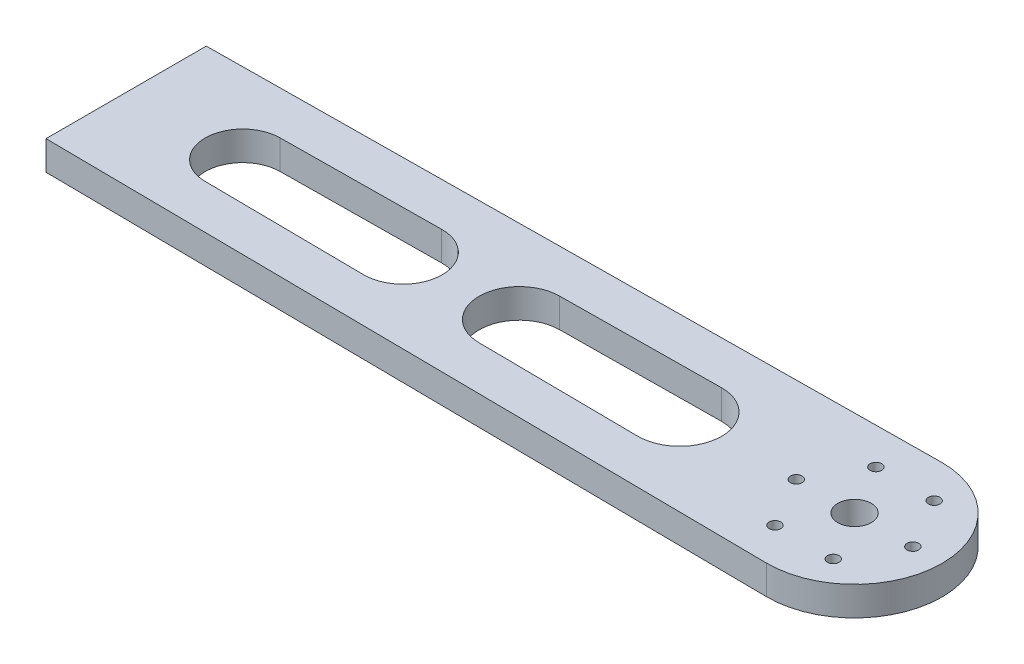
SolidWorks part; units mm, degrees
material "Acrylic (Medium-high impact)"
ref_plane "Front Plane" through (0, 0, 0) normal (0, 0, 1) x (1, 0, 0)
ref_plane "Top Plane" through (0, 0, 0) normal (0, 1, 0) x (1, 0, 0)
ref_plane "Right Plane" through (0, 0, 0) normal (1, 0, 0) x (0, 0, -1)
sketch "Sketch1" plane through (0, 0, 0) normal (0, 1, 0) x (1, 0, 0)
  line L0 (-216.3821, 37.4794) -> (33.318, 39.9538)
  line L1 (-216.3874, -17.5206) -> (33.3122, -20.0432)
  line L2 (-176.5126, 22.8737) -> (-121.518, 23.4187)
  line L3 (-216.3821, 37.4794) -> (-216.3874, -17.5206)
  line L4 (-196.1968, 9.9774) -> (296.6541, 9.9298) construction
  line L5 (-176.5151, -2.9227) -> (-121.5206, -3.4783)
  line L6 (-81.5247, -3.8823) -> (-26.5302, -4.4379)
  line L7 (-81.522, 23.815) -> (-26.5274, 24.36)
  circle A0 centre (33.6152, 9.9552) radius 5.75
  arc A1 (33.3122, -20.0432) -> (33.318, 39.9538) centre (33.6152, 9.9552) ccw
  circle A2 centre (33.6152, 9.9552) radius 20 construction
  circle A3 centre (53.6152, 9.9552) radius 2
  circle A4 centre (43.6152, -7.3653) radius 2
  circle A5 centre (23.6152, -7.3653) radius 2
  circle A6 centre (13.6152, 9.9552) radius 2
  circle A7 centre (23.6152, 27.2757) radius 2
  circle A8 centre (43.6152, 27.2757) radius 2
  arc A9 (-176.5126, 22.8737) -> (-176.5151, -2.9227) centre (-176.3848, 9.9755) ccw
  arc A10 (-26.5302, -4.4379) -> (-26.5274, 24.36) centre (-26.3848, 9.961) ccw
  arc A11 (-121.5206, -3.4783) -> (-121.518, 23.4187) centre (-121.3848, 9.9702) ccw
  arc A12 (-81.522, 23.815) -> (-81.5247, -3.8823) centre (-81.3848, 9.9663) ccw
  point P36 (33.6152, 9.9552)
  dimension "D1" = 60
  dimension "D2" = 11.5
  dimension "D3" = 40
  dimension "D4" = 4
  dimension "D6" = 55
  dimension "D7" = 27.5
  dimension "D8" = 15
  dimension "D9" = 40
  dimension "D10" = 55
  dimension "D11" = 60
  dimension "D12" = 55
  dimension "D22" = 250
  dimension "D5" = 6
extrude "Boss-Extrude1" add sketch "Sketch1" along normal blind 10
